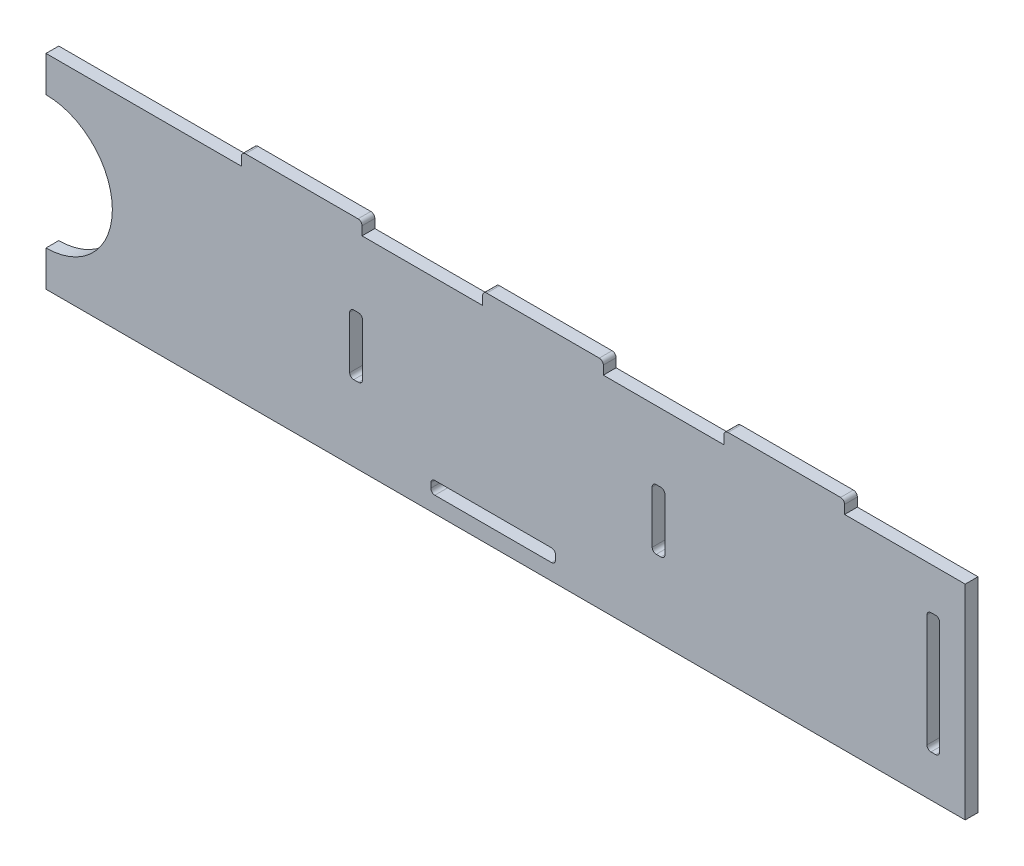
SolidWorks part; units mm, degrees
ref_plane "Front Plane" through (0, 0, 0) normal (0, 0, 1) x (1, 0, 0)
ref_plane "Top Plane" through (0, 0, 0) normal (0, 1, 0) x (1, 0, 0)
ref_plane "Right Plane" through (0, 0, 0) normal (1, 0, 0) x (0, 0, -1)
sketch "Sketch1" plane through (0, 0, 0) normal (0, 0, 1) x (1, 0, 0)
  line L1 (-114.3, -25.4) -> (114.3, -25.4)
  line L2 (-114.3, -25.4) -> (-114.3, 25.4)
  line L3 (-114.3, 25.4) -> (114.3, 25.4)
  line L4 (114.3, -25.4) -> (114.3, 25.4)
  line L5 (-114.3, -25.4) -> (114.3, 25.4) construction
  line L6 (-114.3, 25.4) -> (114.3, -25.4) construction
  point P0 (0, 0)
  dimension "D1" = 228.6
  dimension "D2" = 50.8
extrude "Boss-Extrude1" add sketch "Sketch1" along normal blind 3.175
sketch "Sketch2" plane through (0, 25.4, 0) normal (0, 1, 0) x (1, 0, 0)
  line L0 (114.3, 0) -> (-114.3, 0) construction
  line L1 (84.3, 0) -> (54.3, 0)
  line L2 (84.3, 0) -> (84.3, -3.175)
  line L3 (84.3, -3.175) -> (54.3, -3.175)
  line L4 (54.3, 0) -> (54.3, -3.175)
  line L5 (114.3, -3.175) -> (-114.3, -3.175) construction
  line L6 (114.3, -3.175) -> (114.3, 0) construction
  line L7 (24.3, 0) -> (24.3, -3.175)
  line L8 (24.3, 0) -> (-5.7, 0)
  line L9 (-5.7, 0) -> (-5.7, -3.175)
  line L10 (24.3, -3.175) -> (-5.7, -3.175)
  line L11 (-35.7, 0) -> (-35.7, -3.175)
  line L12 (-35.7, 0) -> (-65.7, 0)
  line L13 (-65.7, 0) -> (-65.7, -3.175)
  line L14 (-35.7, -3.175) -> (-65.7, -3.175)
  point P10 (114.3, -1.5875)
  dimension "D1" = 30
  dimension "D2" = 30
  dimension "D3" = 3
extrude "Boss-Extrude2" add sketch "Sketch2" along normal blind 3.175
sketch "Sketch3" plane through (0, 0, 3.175) normal (0, 0, 1) x (1, 0, 0)
  line L0 (-114.3, 25.4) -> (-114.3, -25.4) construction
  circle A0 centre (-114.3, 0) radius 16.5
  dimension "D1" = 33
extrude "Cut-Extrude1" cut sketch "Sketch3" against normal through all
sketch "Sketch4" plane through (0, 0, 3.175) normal (0, 0, 1) x (1, 0, 0)
  line L0 (107.95, 25.4) -> (107.95, -25.4) construction
  line L1 (114.3, 25.4) -> (84.3, 25.4) construction
  line L2 (-114.3, -25.4) -> (114.3, -25.4) construction
  line L3 (114.3, -25.4) -> (114.3, 25.4) construction
  line L4 (107.95, -15) -> (104.775, -15)
  line L6 (107.95, -15) -> (107.95, 15)
  line L7 (107.95, 15) -> (104.775, 15)
  line L8 (104.775, -15) -> (104.775, 15)
  line L9 (-5.7, 25.4) -> (-35.7, 25.4) construction
  line L10 (39.625, 8.4) -> (36.45, 8.4)
  line L11 (39.625, 8.4) -> (39.625, -6.6)
  line L12 (39.625, -6.6) -> (36.45, -6.6)
  line L13 (36.45, 8.4) -> (36.45, -6.6)
  line L14 (-38.775, 8.4) -> (-35.6, 8.4)
  line L15 (-38.775, 8.4) -> (-38.775, -6.6)
  line L16 (-38.775, -6.6) -> (-35.6, -6.6)
  line L17 (-35.6, 8.4) -> (-35.6, -6.6)
  line L18 (54.3, 25.4) -> (24.3, 25.4) construction
  dimension "D1" = 6.35
  dimension "D2" = 3.175
  dimension "D3" = 3.175
  dimension "D4" = 15
  dimension "D5" = 65.15
  dimension "D6" = 6.35
  dimension "D7" = 72.05
  dimension "D8" = 3.175
  dimension "D9" = 15
  dimension "D10" = 17
  dimension "D11" = 17
extrude "Cut-Extrude2" cut sketch "Sketch4" against normal blind 10
sketch "Sketch5" plane through (0, 0, 3.175) normal (0, 0, 1) x (1, 0, 0)
  line L1 (-114.3, -25.4) -> (114.3, -25.4) construction
  line L2 (12.4, -19.8125) -> (114.3, -19.8125) construction
  line L3 (-18.6, -21.4) -> (12.4, -21.4)
  line L4 (-18.6, -21.4) -> (-18.6, -18.225)
  line L5 (-18.6, -18.225) -> (12.4, -18.225)
  line L6 (12.4, -21.4) -> (12.4, -18.225)
  line L7 (-18.6, -21.4) -> (12.4, -18.225) construction
  line L8 (-18.6, -18.225) -> (12.4, -21.4) construction
  line L9 (114.3, -25.4) -> (114.3, 25.4) construction
  dimension "D1" = 3.175
  dimension "D2" = 31
  dimension "D3" = 4
  dimension "D4" = 101.9
extrude "Cut-Extrude3" cut sketch "Sketch5" against normal blind 10
fillet "Fillet1" radius 1 22 edges at (107.95, -15, 1.5875) (104.775, -15, 1.5875) (104.775, 15, 1.5875) (107.95, 15, 1.5875) (39.625, 8.4, 1.5875) (36.45, 8.4, 1.5875) (39.625, -6.6, 1.5875) (36.45, -6.6, 1.5875) (-18.6, -21.4, 1.5875) (12.4, -21.4, 1.5875) (12.4, -18.225, 1.5875) (-18.6, -18.225, 1.5875) (-38.775, 8.4, 1.5875) (-35.6, 8.4, 1.5875) (-38.775, -6.6, 1.5875) (-35.6, -6.6, 1.5875) (84.3, 28.575, 1.5875) (54.3, 28.575, 1.5875) (24.3, 28.575, 1.5875) (-5.7, 28.575, 1.5875) (-35.7, 28.575, 1.5875) (-65.7, 28.575, 1.5875)
